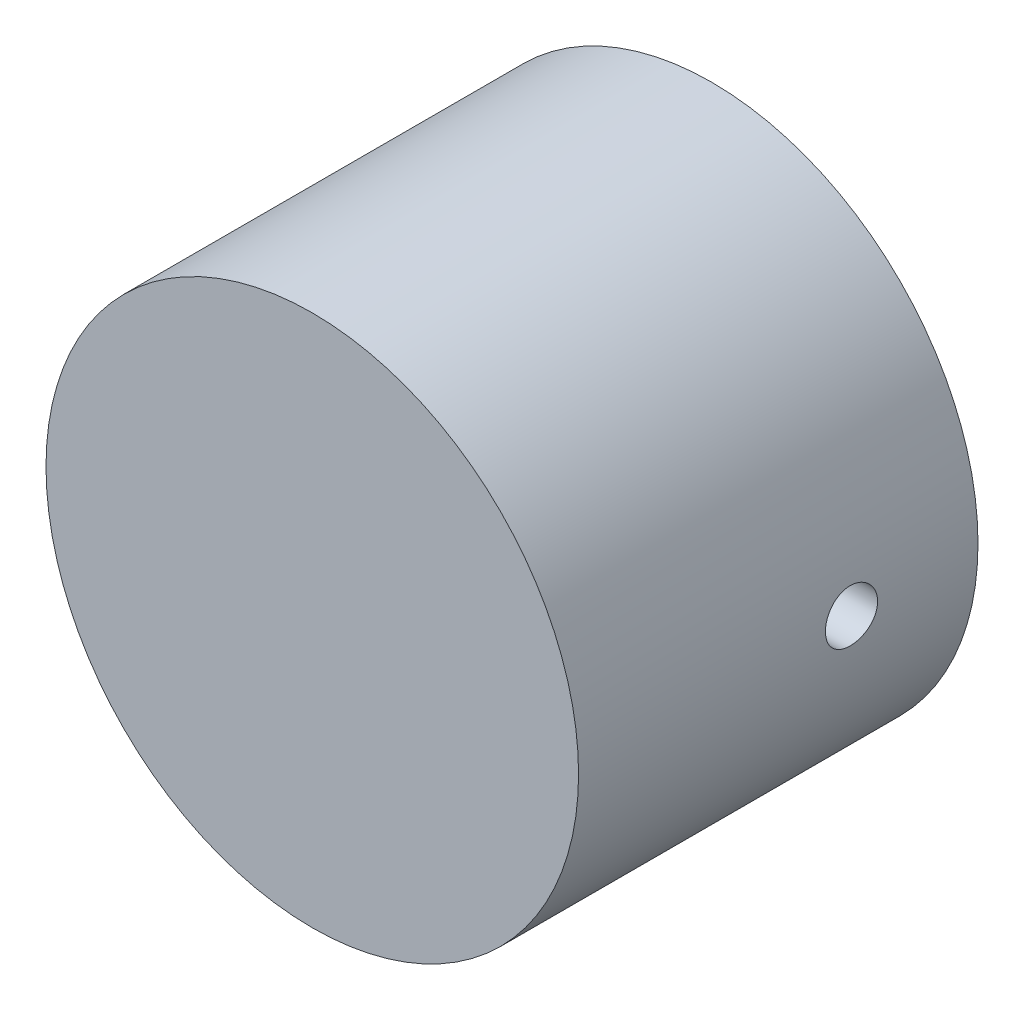
SolidWorks part; units mm, degrees
ref_plane "Front Plane" through (0, 0, 0) normal (0, 0, 1) x (1, 0, 0)
ref_plane "Top Plane" through (0, 0, 0) normal (0, 1, 0) x (1, 0, 0)
ref_plane "Right Plane" through (0, 0, 0) normal (1, 0, 0) x (0, 0, -1)
sketch "Sketch1" plane through (0, 0, 0) normal (0, 0, 1) x (1, 0, 0)
  circle A0 centre (0, 0) radius 12.7
  dimension "D1" = 25.4
extrude "Boss-Extrude1" add sketch "Sketch1" against normal blind 19.05
shell "Shell1" thickness 3.175
ref_plane "Plane1" through (0, 0, -13.0175) normal (0, 0, -1) x (-1, 0, 0)
sketch "Sketch3" plane through (0, 0, -13.0175) normal (0, 0, -1) x (-1, 0, 0)
  line L0 (12.7, 0) -> (-12.7, 0) construction
  circle A0 centre (0, 0) radius 12.7 construction
sketch "Sketch4" plane through (0, 0, 0) normal (1, 0, 0) x (0, 0, -1)
  line L0 (13.0175, -17.4625) -> (13.0175, 17.4625) construction
  circle A0 centre (13.0175, 0) radius 1.2446
  dimension "D1" = 2.4892
extrude "Cut-Extrude1" cut sketch "Sketch4" against normal through all both and the other way through all
ref_plane "Plane2" through (0, 0, -17.78) normal (0, 0, -1) x (-1, 0, 0)
sketch "Sketch7" plane through (0, 0, -17.78) normal (0, 0, -1) x (-1, 0, 0)
  circle A0 centre (0, 0) radius 10.8712
  circle A1 centre (0, 0) radius 9.525 construction
  circle A2 centre (0, 0) radius 9.525
  dimension "D1" = 21.7424
extrude "Cut-Extrude2" cut sketch "Sketch7" against normal blind 2.3622
